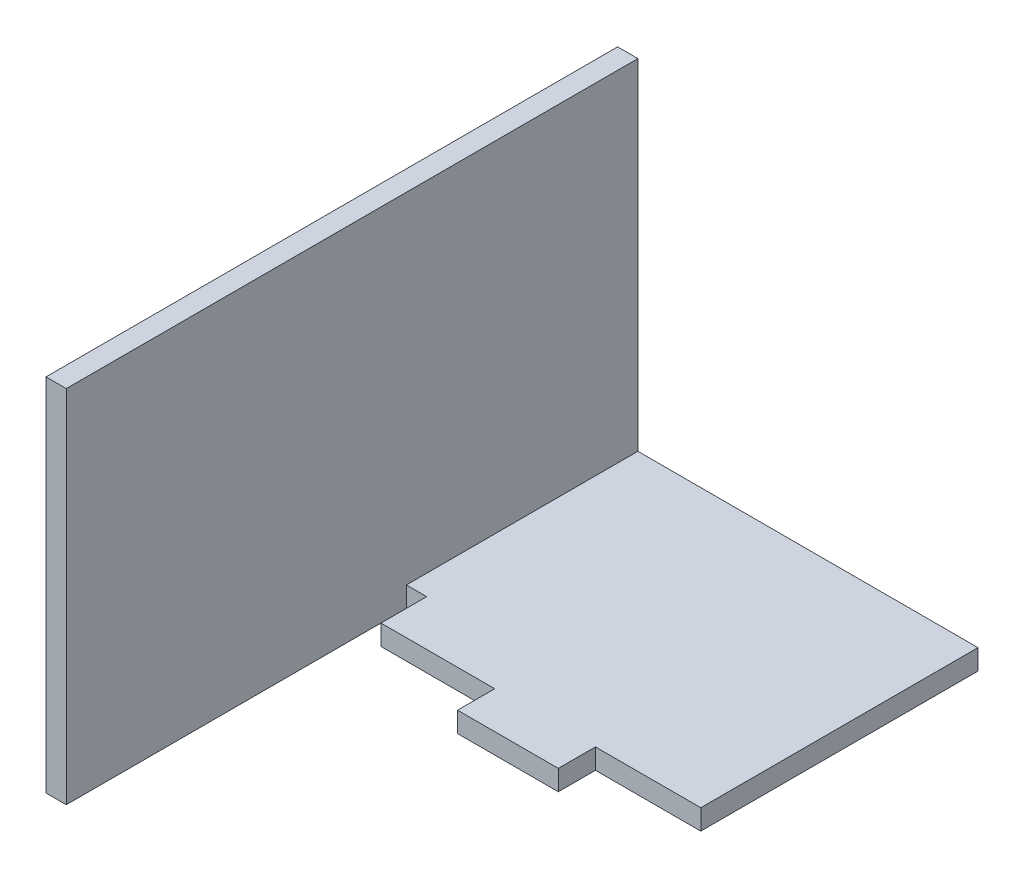
SolidWorks part; units mm, degrees
ref_plane "Front" through (0, 0, 0) normal (0, 0, 1) x (1, 0, 0)
ref_plane "Top" through (0, 0, 0) normal (0, 1, 0) x (1, 0, 0)
ref_plane "Right" through (0, 0, 0) normal (1, 0, 0) x (0, 0, -1)
sketch "Sketch1" plane through (0, 0, 0) normal (0, 0, 1) x (1, 0, 0)
  line L0 (0, 0) -> (0, -25.22)
  line L1 (25.22, -25.22) -> (0, -25.22)
  line L2 (25.22, -25.22) -> (25.22, -23.8)
  line L3 (25.22, -23.8) -> (1.42, -23.8)
  line L4 (1.42, 0) -> (1.42, -23.8)
  line L5 (1.42, 0) -> (0, 0)
extrude "Extrude1" add sketch "Sketch1" along normal blind 40
sketch "Sketch3" plane through (0, -23.8, 0) normal (0, 1, 0) x (-1, 0, 0)
  line L0 (-1.42, 40) -> (-1.42, 16.2)
  line L1 (-1.42, 40) -> (-1.42, 0) construction
  line L2 (-1.42, 16.2) -> (-2.84, 16.2)
  line L3 (-2.84, 16.2) -> (-2.84, 19.4)
  line L4 (-2.84, 19.4) -> (-10.8, 19.4)
  line L5 (-10.8, 19.4) -> (-10.8, 22)
  line L6 (-10.8, 22) -> (-17.85, 22)
  line L7 (-17.85, 22) -> (-17.85, 19.4)
  line L8 (-17.85, 19.4) -> (-25.22, 19.4)
  line L9 (-25.22, 40) -> (-25.22, 0) construction
  line L10 (-25.22, 19.4) -> (-25.22, 40)
  line L11 (-25.22, 40) -> (-1.42, 40)
extrude "Cut-Extrude3" cut sketch "Sketch3" against normal through all
